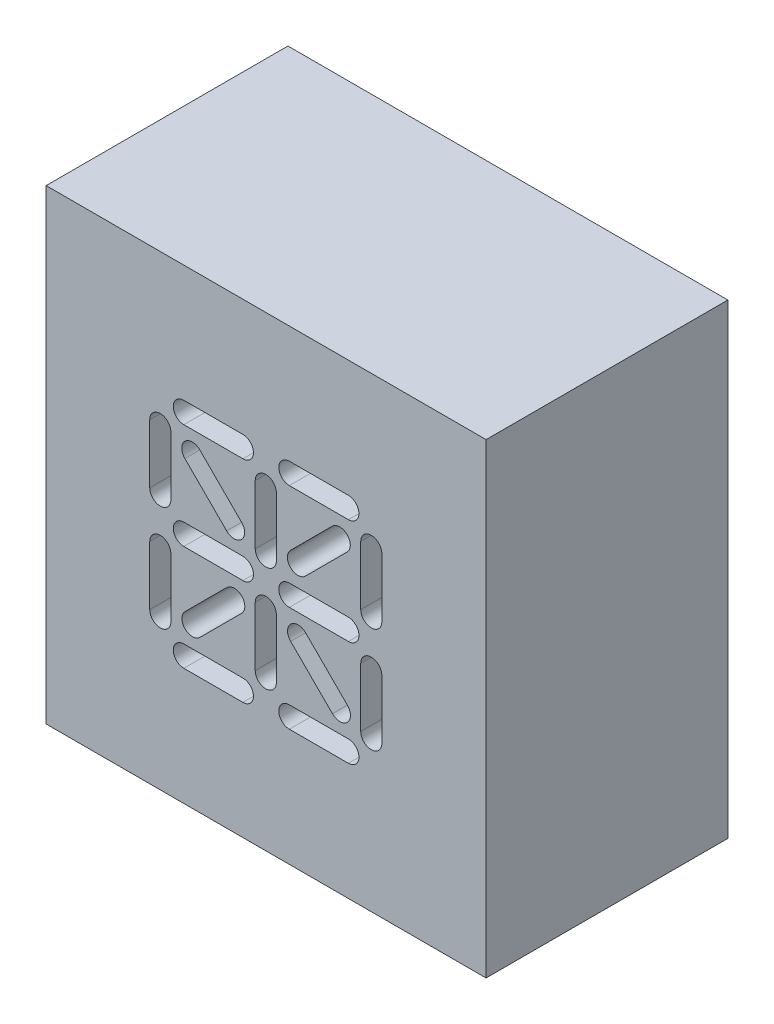
SolidWorks part; units mm, degrees
material "ABS PC"
ref_plane "Front Plane" through (0, 0, 0) normal (0, 0, 1) x (1, 0, 0)
ref_plane "Top Plane" through (0, 0, 0) normal (0, 1, 0) x (1, 0, 0)
ref_plane "Right Plane" through (0, 0, 0) normal (1, 0, 0) x (0, 0, -1)
sketch "Sketch1" plane through (0, 0, 0) normal (0, 0, 1) x (1, 0, 0)
  line L0 (265.9975, 197.0179) -> (342.1693, 194.9479) construction
  line L1 (297.418, 228.3826) -> (298.307, 228.3826) construction
  line L2 (297.418, 228.3826) -> (300.593, 228.3826) construction
  line L3 (302.371, 228.3826) -> (302.371, 231.5576) construction
  line L4 (296.7097, 229.0811) -> (296.7097, 229.9701) construction
  line L5 (296.7097, 230.8591) -> (296.7097, 234.0341) construction
  line L6 (296.7097, 234.0341) -> (299.8847, 234.0341) construction
  line L7 (296.7097, 234.0341) -> (297.0639, 234.3834) construction
  line L8 (296.7097, 234.0341) -> (297.418, 234.7326) construction
  line L9 (299.196, 231.5576) -> (300.593, 231.5576) construction
  line L10 (297.0639, 234.3834) -> (299.5404, 231.9069) construction
  line L11 (296.7097, 232.2561) -> (296.7097, 230.8591) construction
  line L12 (297.418, 231.5576) -> (296.7097, 231.5576) construction
  line L13 (299.8847, 232.2561) -> (299.196, 231.5576) construction
  line L14 (299.8945, 231.5576) -> (298.9307, 232.5165) construction
  line L15 (299.8945, 231.5576) -> (300.8534, 232.5214) construction
  line L16 (297.418, 234.7326) -> (307.578, 234.7326) construction
  line L17 (293.5347, 230.4146) -> (293.5347, 229.5256) construction
  line L18 (293.5347, 232.7006) -> (293.5347, 230.4146) construction
  line L19 (335.8892, 225.6039) -> (291.1852, 225.6039)
  line L20 (335.8892, 225.6039) -> (335.8892, 237.5114)
  line L21 (335.8892, 237.5114) -> (291.1852, 237.5114)
  line L22 (291.1852, 225.6039) -> (291.1852, 237.5114)
  line L23 (335.8892, 225.6039) -> (291.1852, 237.5114) construction
  line L24 (335.8892, 237.5114) -> (291.1852, 225.6039) construction
  line L25 (333.5397, 232.2561) -> (333.5397, 230.8591) construction
  line L26 (293.5347, 231.5576) -> (333.5397, 231.5576) construction
  line L27 (297.418, 228.3826) -> (299.196, 228.3826) construction
  line L32 (297.418, 228.7001) -> (299.196, 228.7001)
  line L33 (297.418, 228.0651) -> (299.196, 228.0651)
  line L34 (300.593, 228.3826) -> (302.371, 228.3826) construction
  line L35 (300.593, 228.7001) -> (302.371, 228.7001)
  line L36 (300.593, 228.0651) -> (302.371, 228.0651)
  line L37 (302.1155, 229.3415) -> (300.8582, 230.5987) construction
  line L38 (301.891, 229.117) -> (300.6337, 230.3742)
  line L39 (302.34, 229.566) -> (301.0827, 230.8233)
  line L40 (299.8847, 229.0811) -> (299.8847, 230.8591) construction
  line L41 (299.5672, 229.0811) -> (299.5672, 230.8591)
  line L42 (300.2022, 229.0811) -> (300.2022, 230.8591)
  line L43 (298.9356, 230.5939) -> (297.6784, 229.3366) construction
  line L44 (299.1601, 230.3694) -> (297.9029, 229.1121)
  line L45 (298.7111, 230.8184) -> (297.4539, 229.5611)
  line L46 (296.7097, 229.0811) -> (296.7097, 230.8591) construction
  line L47 (296.3922, 229.0811) -> (296.3922, 230.8591)
  line L48 (297.0272, 229.0811) -> (297.0272, 230.8591)
  line L49 (303.0597, 230.8591) -> (303.0597, 229.0811) construction
  line L50 (303.3772, 230.8591) -> (303.3772, 229.0811)
  line L51 (302.7422, 230.8591) -> (302.7422, 229.0811)
  line L52 (302.371, 231.5576) -> (300.593, 231.5576) construction
  line L53 (302.371, 231.2401) -> (300.593, 231.2401)
  line L54 (302.371, 231.8751) -> (300.593, 231.8751)
  line L55 (303.0597, 234.0341) -> (303.0597, 232.2561) construction
  line L56 (303.3772, 234.0341) -> (303.3772, 232.2561)
  line L57 (302.7422, 234.0341) -> (302.7422, 232.2561)
  line L58 (302.1106, 233.7786) -> (300.8534, 232.5214) construction
  line L59 (302.3351, 233.5541) -> (301.0779, 232.2969)
  line L60 (301.8861, 234.0031) -> (300.6289, 232.7459)
  line L61 (302.371, 234.7326) -> (300.593, 234.7326) construction
  line L62 (302.371, 234.4151) -> (300.593, 234.4151)
  line L63 (302.371, 235.0501) -> (300.593, 235.0501)
  line L64 (299.8847, 234.0341) -> (299.8847, 232.2561) construction
  line L65 (300.2022, 234.0341) -> (300.2022, 232.2561)
  line L66 (299.5672, 234.0341) -> (299.5672, 232.2561)
  line L67 (297.418, 231.5576) -> (299.196, 231.5576) construction
  line L68 (297.418, 231.8751) -> (299.196, 231.8751)
  line L69 (297.418, 231.2401) -> (299.196, 231.2401)
  line L70 (298.9307, 232.5165) -> (297.6735, 233.7737) construction
  line L71 (298.7062, 232.292) -> (297.449, 233.5492)
  line L72 (299.1552, 232.741) -> (297.898, 233.9983)
  line L73 (296.7097, 232.2561) -> (296.7097, 234.0341) construction
  line L74 (296.3922, 232.2561) -> (296.3922, 234.0341)
  line L75 (297.0272, 232.2561) -> (297.0272, 234.0341)
  line L76 (297.418, 234.7326) -> (299.196, 234.7326) construction
  line L77 (297.418, 235.0501) -> (299.196, 235.0501)
  line L78 (297.418, 234.4151) -> (299.196, 234.4151)
  line L79 (293.5347, 232.7006) -> (293.5347, 233.5896) construction
  line L80 (293.2172, 232.7006) -> (293.2172, 233.5896)
  line L81 (293.8522, 232.7006) -> (293.8522, 233.5896)
  line L82 (293.5347, 230.4146) -> (293.5347, 229.5256) construction
  line L83 (293.8522, 230.4146) -> (293.8522, 229.5256)
  line L84 (293.2172, 230.4146) -> (293.2172, 229.5256)
  line L85 (307.578, 228.3826) -> (309.356, 228.3826) construction
  line L86 (307.578, 228.7001) -> (309.356, 228.7001)
  line L87 (307.578, 228.0651) -> (309.356, 228.0651)
  line L88 (310.753, 228.3826) -> (312.531, 228.3826) construction
  line L89 (310.753, 228.7001) -> (312.531, 228.7001)
  line L90 (310.753, 228.0651) -> (312.531, 228.0651)
  line L91 (312.2755, 229.3415) -> (311.0182, 230.5987) construction
  line L92 (312.051, 229.117) -> (310.7937, 230.3742)
  line L93 (312.5, 229.566) -> (311.2427, 230.8233)
  line L94 (310.0447, 229.0811) -> (310.0447, 230.8591) construction
  line L95 (309.7272, 229.0811) -> (309.7272, 230.8591)
  line L96 (310.3622, 229.0811) -> (310.3622, 230.8591)
  line L97 (309.0956, 230.5939) -> (307.8384, 229.3366) construction
  line L98 (309.3201, 230.3694) -> (308.0629, 229.1121)
  line L99 (308.8711, 230.8184) -> (307.6139, 229.5611)
  line L100 (306.8697, 229.0811) -> (306.8697, 230.8591) construction
  line L101 (306.5522, 229.0811) -> (306.5522, 230.8591)
  line L102 (307.1872, 229.0811) -> (307.1872, 230.8591)
  line L103 (313.2197, 230.8591) -> (313.2197, 229.0811) construction
  line L104 (313.5372, 230.8591) -> (313.5372, 229.0811)
  line L105 (312.9022, 230.8591) -> (312.9022, 229.0811)
  line L106 (312.531, 231.5576) -> (310.753, 231.5576) construction
  line L107 (312.531, 231.2401) -> (310.753, 231.2401)
  line L108 (312.531, 231.8751) -> (310.753, 231.8751)
  line L109 (313.2197, 234.0341) -> (313.2197, 232.2561) construction
  line L110 (313.5372, 234.0341) -> (313.5372, 232.2561)
  line L111 (312.9022, 234.0341) -> (312.9022, 232.2561)
  line L112 (312.2706, 233.7786) -> (311.0134, 232.5214) construction
  line L113 (312.4951, 233.5541) -> (311.2379, 232.2969)
  line L114 (312.0461, 234.0031) -> (310.7889, 232.7459)
  line L115 (312.531, 234.7326) -> (310.753, 234.7326) construction
  line L116 (312.531, 234.4151) -> (310.753, 234.4151)
  line L117 (312.531, 235.0501) -> (310.753, 235.0501)
  line L118 (310.0447, 234.0341) -> (310.0447, 232.2561) construction
  line L119 (310.3622, 234.0341) -> (310.3622, 232.2561)
  line L120 (309.7272, 234.0341) -> (309.7272, 232.2561)
  line L121 (307.578, 231.5576) -> (309.356, 231.5576) construction
  line L122 (307.578, 231.8751) -> (309.356, 231.8751)
  line L123 (307.578, 231.2401) -> (309.356, 231.2401)
  line L124 (309.0907, 232.5165) -> (307.8335, 233.7737) construction
  line L125 (308.8662, 232.292) -> (307.609, 233.5492)
  line L126 (309.3152, 232.741) -> (308.058, 233.9983)
  line L127 (306.8697, 232.2561) -> (306.8697, 234.0341) construction
  line L128 (306.5522, 232.2561) -> (306.5522, 234.0341)
  line L129 (307.1872, 232.2561) -> (307.1872, 234.0341)
  line L130 (307.578, 234.7326) -> (309.356, 234.7326) construction
  line L131 (307.578, 235.0501) -> (309.356, 235.0501)
  line L132 (307.578, 234.4151) -> (309.356, 234.4151)
  line L133 (317.738, 228.3826) -> (319.516, 228.3826) construction
  line L134 (317.738, 228.7001) -> (319.516, 228.7001)
  line L135 (317.738, 228.0651) -> (319.516, 228.0651)
  line L136 (320.913, 228.3826) -> (322.691, 228.3826) construction
  line L137 (320.913, 228.7001) -> (322.691, 228.7001)
  line L138 (320.913, 228.0651) -> (322.691, 228.0651)
  line L139 (322.4355, 229.3415) -> (321.1782, 230.5987) construction
  line L140 (322.211, 229.117) -> (320.9537, 230.3742)
  line L141 (322.66, 229.566) -> (321.4027, 230.8233)
  line L142 (320.2047, 229.0811) -> (320.2047, 230.8591) construction
  line L143 (319.8872, 229.0811) -> (319.8872, 230.8591)
  line L144 (320.5222, 229.0811) -> (320.5222, 230.8591)
  line L145 (319.2556, 230.5939) -> (317.9984, 229.3366) construction
  line L146 (319.4801, 230.3694) -> (318.2229, 229.1121)
  line L147 (319.0311, 230.8184) -> (317.7739, 229.5611)
  line L148 (317.0297, 229.0811) -> (317.0297, 230.8591) construction
  line L149 (316.7122, 229.0811) -> (316.7122, 230.8591)
  line L150 (317.3472, 229.0811) -> (317.3472, 230.8591)
  line L151 (323.3797, 230.8591) -> (323.3797, 229.0811) construction
  line L152 (323.6972, 230.8591) -> (323.6972, 229.0811)
  line L153 (323.0622, 230.8591) -> (323.0622, 229.0811)
  line L154 (322.691, 231.5576) -> (320.913, 231.5576) construction
  line L155 (322.691, 231.2401) -> (320.913, 231.2401)
  line L156 (322.691, 231.8751) -> (320.913, 231.8751)
  line L157 (323.3797, 234.0341) -> (323.3797, 232.2561) construction
  line L158 (323.6972, 234.0341) -> (323.6972, 232.2561)
  line L159 (323.0622, 234.0341) -> (323.0622, 232.2561)
  line L160 (322.4306, 233.7786) -> (321.1734, 232.5214) construction
  line L161 (322.6551, 233.5541) -> (321.3979, 232.2969)
  line L162 (322.2061, 234.0031) -> (320.9489, 232.7459)
  line L163 (322.691, 234.7326) -> (320.913, 234.7326) construction
  line L164 (322.691, 234.4151) -> (320.913, 234.4151)
  line L165 (322.691, 235.0501) -> (320.913, 235.0501)
  line L166 (320.2047, 234.0341) -> (320.2047, 232.2561) construction
  line L167 (320.5222, 234.0341) -> (320.5222, 232.2561)
  line L168 (319.8872, 234.0341) -> (319.8872, 232.2561)
  line L169 (317.738, 231.5576) -> (319.516, 231.5576) construction
  line L170 (317.738, 231.8751) -> (319.516, 231.8751)
  line L171 (317.738, 231.2401) -> (319.516, 231.2401)
  line L172 (319.2507, 232.5165) -> (317.9935, 233.7737) construction
  line L173 (319.0262, 232.292) -> (317.769, 233.5492)
  line L174 (319.4752, 232.741) -> (318.218, 233.9983)
  line L175 (317.0297, 232.2561) -> (317.0297, 234.0341) construction
  line L176 (316.7122, 232.2561) -> (316.7122, 234.0341)
  line L177 (317.3472, 232.2561) -> (317.3472, 234.0341)
  line L178 (317.738, 234.7326) -> (319.516, 234.7326) construction
  line L179 (317.738, 235.0501) -> (319.516, 235.0501)
  line L180 (317.738, 234.4151) -> (319.516, 234.4151)
  line L181 (327.898, 228.3826) -> (329.676, 228.3826) construction
  line L182 (327.898, 228.7001) -> (329.676, 228.7001)
  line L183 (327.898, 228.0651) -> (329.676, 228.0651)
  line L184 (331.073, 228.3826) -> (332.851, 228.3826) construction
  line L185 (331.073, 228.7001) -> (332.851, 228.7001)
  line L186 (331.073, 228.0651) -> (332.851, 228.0651)
  line L187 (332.5955, 229.3415) -> (331.3382, 230.5987) construction
  line L188 (332.371, 229.117) -> (331.1137, 230.3742)
  line L189 (332.82, 229.566) -> (331.5627, 230.8233)
  line L190 (330.3647, 229.0811) -> (330.3647, 230.8591) construction
  line L191 (330.0472, 229.0811) -> (330.0472, 230.8591)
  line L192 (330.6822, 229.0811) -> (330.6822, 230.8591)
  line L193 (329.4156, 230.5939) -> (328.1584, 229.3366) construction
  line L194 (329.6401, 230.3694) -> (328.3829, 229.1121)
  line L195 (329.1911, 230.8184) -> (327.9339, 229.5611)
  line L196 (327.1897, 229.0811) -> (327.1897, 230.8591) construction
  line L197 (326.8722, 229.0811) -> (326.8722, 230.8591)
  line L198 (327.5072, 229.0811) -> (327.5072, 230.8591)
  line L199 (333.5397, 230.8591) -> (333.5397, 229.0811) construction
  line L200 (333.8572, 230.8591) -> (333.8572, 229.0811)
  line L201 (333.2222, 230.8591) -> (333.2222, 229.0811)
  line L202 (332.851, 231.5576) -> (331.073, 231.5576) construction
  line L203 (332.851, 231.2401) -> (331.073, 231.2401)
  line L204 (332.851, 231.8751) -> (331.073, 231.8751)
  line L205 (333.5397, 234.0341) -> (333.5397, 232.2561) construction
  line L206 (333.8572, 234.0341) -> (333.8572, 232.2561)
  line L207 (333.2222, 234.0341) -> (333.2222, 232.2561)
  line L208 (332.5906, 233.7786) -> (331.3334, 232.5214) construction
  line L209 (332.8151, 233.5541) -> (331.5579, 232.2969)
  line L210 (332.3661, 234.0031) -> (331.1089, 232.7459)
  line L211 (332.851, 234.7326) -> (331.073, 234.7326) construction
  line L212 (332.851, 234.4151) -> (331.073, 234.4151)
  line L213 (332.851, 235.0501) -> (331.073, 235.0501)
  line L214 (330.3647, 234.0341) -> (330.3647, 232.2561) construction
  line L215 (330.6822, 234.0341) -> (330.6822, 232.2561)
  line L216 (330.0472, 234.0341) -> (330.0472, 232.2561)
  line L217 (327.898, 231.5576) -> (329.676, 231.5576) construction
  line L218 (327.898, 231.8751) -> (329.676, 231.8751)
  line L219 (327.898, 231.2401) -> (329.676, 231.2401)
  line L220 (329.4107, 232.5165) -> (328.1535, 233.7737) construction
  line L221 (329.1862, 232.292) -> (327.929, 233.5492)
  line L222 (329.6352, 232.741) -> (328.378, 233.9983)
  line L223 (327.1897, 232.2561) -> (327.1897, 234.0341) construction
  line L224 (326.8722, 232.2561) -> (326.8722, 234.0341)
  line L225 (327.5072, 232.2561) -> (327.5072, 234.0341)
  line L226 (327.898, 234.7326) -> (329.676, 234.7326) construction
  line L227 (327.898, 235.0501) -> (329.676, 235.0501)
  line L228 (327.898, 234.4151) -> (329.676, 234.4151)
  line L229 (296.7097, 229.0811) -> (306.8697, 229.0811) construction
  circle A0 centre (297.418, 228.3826) radius 0.3175 construction
  circle A3 centre (298.307, 228.3826) radius 0.3175 construction
  circle A4 centre (299.196, 228.3826) radius 0.3175 construction
  circle A5 centre (300.593, 228.3826) radius 0.3175 construction
  circle A6 centre (301.482, 228.3826) radius 0.3175 construction
  circle A7 centre (302.371, 228.3826) radius 0.3175 construction
  circle A8 centre (302.371, 231.5576) radius 0.3175 construction
  circle A9 centre (301.482, 231.5576) radius 0.3175 construction
  circle A10 centre (300.593, 231.5576) radius 0.3175 construction
  circle A11 centre (299.196, 231.5576) radius 0.3175 construction
  circle A12 centre (298.307, 231.5576) radius 0.3175 construction
  circle A13 centre (297.418, 231.5576) radius 0.3175 construction
  circle A14 centre (302.371, 234.7326) radius 0.3175 construction
  circle A15 centre (301.482, 234.7326) radius 0.3175 construction
  circle A16 centre (300.593, 234.7326) radius 0.3175 construction
  circle A17 centre (299.196, 234.7326) radius 0.3175 construction
  circle A18 centre (298.307, 234.7326) radius 0.3175 construction
  circle A19 centre (297.418, 234.7326) radius 0.3175 construction
  circle A20 centre (296.7097, 229.0811) radius 0.3175 construction
  circle A21 centre (296.7097, 229.9701) radius 0.3175 construction
  circle A22 centre (296.7097, 230.8591) radius 0.3175 construction
  circle A23 centre (296.7097, 234.0341) radius 0.3175 construction
  circle A24 centre (296.7097, 233.1451) radius 0.3175 construction
  circle A25 centre (296.7097, 232.2561) radius 0.3175 construction
  circle A26 centre (299.8847, 234.0341) radius 0.3175 construction
  circle A27 centre (299.8847, 233.1451) radius 0.3175 construction
  circle A28 centre (299.8847, 232.2561) radius 0.3175 construction
  circle A29 centre (299.8847, 230.8591) radius 0.3175 construction
  circle A30 centre (299.8847, 229.9701) radius 0.3175 construction
  circle A31 centre (299.8847, 229.0811) radius 0.3175 construction
  circle A32 centre (297.6735, 233.7737) radius 0.3175 construction
  circle A33 centre (298.3021, 233.1451) radius 0.3175 construction
  circle A34 centre (298.9307, 232.5165) radius 0.3175 construction
  circle A35 centre (303.0597, 234.0341) radius 0.3175 construction
  circle A36 centre (303.0597, 233.1451) radius 0.3175 construction
  circle A37 centre (303.0597, 232.2561) radius 0.3175 construction
  circle A38 centre (303.0597, 230.8591) radius 0.3175 construction
  circle A39 centre (303.0597, 229.9701) radius 0.3175 construction
  circle A40 centre (303.0597, 229.0811) radius 0.3175 construction
  circle A41 centre (300.8534, 232.5214) radius 0.3175 construction
  circle A42 centre (301.482, 233.15) radius 0.3175 construction
  circle A43 centre (302.1106, 233.7786) radius 0.3175 construction
  circle A44 centre (300.8582, 230.5987) radius 0.3175 construction
  circle A45 centre (301.4869, 229.9701) radius 0.3175 construction
  circle A46 centre (302.1155, 229.3415) radius 0.3175 construction
  circle A47 centre (298.9356, 230.5939) radius 0.3175 construction
  circle A48 centre (298.307, 229.9653) radius 0.3175 construction
  circle A49 centre (297.6784, 229.3366) radius 0.3175 construction
  circle A50 centre (307.578, 234.7326) radius 0.3175 construction
  circle A51 centre (306.8697, 234.0341) radius 0.3175 construction
  circle A52 centre (306.8697, 233.1451) radius 0.3175 construction
  circle A53 centre (306.8697, 232.2561) radius 0.3175 construction
  circle A54 centre (308.467, 234.7326) radius 0.3175 construction
  circle A55 centre (309.356, 234.7326) radius 0.3175 construction
  circle A56 centre (310.753, 234.7326) radius 0.3175 construction
  circle A57 centre (311.642, 234.7326) radius 0.3175 construction
  circle A58 centre (312.531, 234.7326) radius 0.3175 construction
  circle A59 centre (313.2197, 234.0341) radius 0.3175 construction
  circle A60 centre (313.2197, 233.1451) radius 0.3175 construction
  circle A61 centre (313.2197, 232.2561) radius 0.3175 construction
  circle A62 centre (313.2197, 230.8591) radius 0.3175 construction
  circle A63 centre (313.2197, 229.9701) radius 0.3175 construction
  circle A64 centre (313.2197, 229.0811) radius 0.3175 construction
  circle A65 centre (312.531, 228.3826) radius 0.3175 construction
  circle A66 centre (311.642, 228.3826) radius 0.3175 construction
  circle A67 centre (310.753, 228.3826) radius 0.3175 construction
  circle A68 centre (309.356, 228.3826) radius 0.3175 construction
  circle A69 centre (308.467, 228.3826) radius 0.3175 construction
  circle A70 centre (307.578, 228.3826) radius 0.3175 construction
  circle A71 centre (306.8697, 229.0811) radius 0.3175 construction
  circle A72 centre (306.8697, 229.9701) radius 0.3175 construction
  circle A73 centre (306.8697, 230.8591) radius 0.3175 construction
  circle A74 centre (307.578, 231.5576) radius 0.3175 construction
  circle A75 centre (308.467, 231.5576) radius 0.3175 construction
  circle A76 centre (309.356, 231.5576) radius 0.3175 construction
  circle A77 centre (310.753, 231.5576) radius 0.3175 construction
  circle A78 centre (311.642, 231.5576) radius 0.3175 construction
  circle A79 centre (312.531, 231.5576) radius 0.3175 construction
  circle A80 centre (312.2706, 233.7786) radius 0.3175 construction
  circle A81 centre (311.642, 233.15) radius 0.3175 construction
  circle A82 centre (311.0134, 232.5214) radius 0.3175 construction
  circle A83 centre (310.0447, 232.2561) radius 0.3175 construction
  circle A84 centre (310.0447, 233.1451) radius 0.3175 construction
  circle A85 centre (310.0447, 234.0341) radius 0.3175 construction
  circle A86 centre (309.0907, 232.5165) radius 0.3175 construction
  circle A87 centre (308.4621, 233.1451) radius 0.3175 construction
  circle A88 centre (307.8335, 233.7737) radius 0.3175 construction
  circle A89 centre (307.8384, 229.3366) radius 0.3175 construction
  circle A90 centre (308.467, 229.9653) radius 0.3175 construction
  circle A91 centre (309.0956, 230.5939) radius 0.3175 construction
  circle A92 centre (310.0447, 230.8591) radius 0.3175 construction
  circle A93 centre (310.0447, 229.9701) radius 0.3175 construction
  circle A94 centre (310.0447, 229.0811) radius 0.3175 construction
  circle A95 centre (312.2755, 229.3415) radius 0.3175 construction
  circle A96 centre (311.6469, 229.9701) radius 0.3175 construction
  circle A97 centre (311.0182, 230.5987) radius 0.3175 construction
  circle A98 centre (317.738, 234.7326) radius 0.3175 construction
  circle A99 centre (317.0297, 234.0341) radius 0.3175 construction
  circle A100 centre (317.0297, 233.1451) radius 0.3175 construction
  circle A101 centre (317.0297, 232.2561) radius 0.3175 construction
  circle A102 centre (318.627, 234.7326) radius 0.3175 construction
  circle A103 centre (319.516, 234.7326) radius 0.3175 construction
  circle A104 centre (320.913, 234.7326) radius 0.3175 construction
  circle A105 centre (321.802, 234.7326) radius 0.3175 construction
  circle A106 centre (322.691, 234.7326) radius 0.3175 construction
  circle A107 centre (323.3797, 234.0341) radius 0.3175 construction
  circle A108 centre (323.3797, 233.1451) radius 0.3175 construction
  circle A109 centre (323.3797, 232.2561) radius 0.3175 construction
  circle A110 centre (323.3797, 230.8591) radius 0.3175 construction
  circle A111 centre (323.3797, 229.9701) radius 0.3175 construction
  circle A112 centre (323.3797, 229.0811) radius 0.3175 construction
  circle A113 centre (322.691, 228.3826) radius 0.3175 construction
  circle A114 centre (321.802, 228.3826) radius 0.3175 construction
  circle A115 centre (320.913, 228.3826) radius 0.3175 construction
  circle A116 centre (319.516, 228.3826) radius 0.3175 construction
  circle A117 centre (318.627, 228.3826) radius 0.3175 construction
  circle A118 centre (317.738, 228.3826) radius 0.3175 construction
  circle A119 centre (317.0297, 229.0811) radius 0.3175 construction
  circle A120 centre (317.0297, 229.9701) radius 0.3175 construction
  circle A121 centre (317.0297, 230.8591) radius 0.3175 construction
  circle A122 centre (317.738, 231.5576) radius 0.3175 construction
  circle A123 centre (318.627, 231.5576) radius 0.3175 construction
  circle A124 centre (319.516, 231.5576) radius 0.3175 construction
  circle A125 centre (320.913, 231.5576) radius 0.3175 construction
  circle A126 centre (321.802, 231.5576) radius 0.3175 construction
  circle A127 centre (322.691, 231.5576) radius 0.3175 construction
  circle A128 centre (322.4306, 233.7786) radius 0.3175 construction
  circle A129 centre (321.802, 233.15) radius 0.3175 construction
  circle A130 centre (321.1734, 232.5214) radius 0.3175 construction
  circle A131 centre (320.2047, 232.2561) radius 0.3175 construction
  circle A132 centre (320.2047, 233.1451) radius 0.3175 construction
  circle A133 centre (320.2047, 234.0341) radius 0.3175 construction
  circle A134 centre (319.2507, 232.5165) radius 0.3175 construction
  circle A135 centre (318.6221, 233.1451) radius 0.3175 construction
  circle A136 centre (317.9935, 233.7737) radius 0.3175 construction
  circle A137 centre (317.9984, 229.3366) radius 0.3175 construction
  circle A138 centre (318.627, 229.9653) radius 0.3175 construction
  circle A139 centre (319.2556, 230.5939) radius 0.3175 construction
  circle A140 centre (320.2047, 230.8591) radius 0.3175 construction
  circle A141 centre (320.2047, 229.9701) radius 0.3175 construction
  circle A142 centre (320.2047, 229.0811) radius 0.3175 construction
  circle A143 centre (322.4355, 229.3415) radius 0.3175 construction
  circle A144 centre (321.8069, 229.9701) radius 0.3175 construction
  circle A145 centre (321.1782, 230.5987) radius 0.3175 construction
  circle A146 centre (327.898, 234.7326) radius 0.3175 construction
  circle A147 centre (327.1897, 234.0341) radius 0.3175 construction
  circle A148 centre (327.1897, 233.1451) radius 0.3175 construction
  circle A149 centre (327.1897, 232.2561) radius 0.3175 construction
  circle A150 centre (328.787, 234.7326) radius 0.3175 construction
  circle A151 centre (329.676, 234.7326) radius 0.3175 construction
  circle A152 centre (331.073, 234.7326) radius 0.3175 construction
  circle A153 centre (331.962, 234.7326) radius 0.3175 construction
  circle A154 centre (332.851, 234.7326) radius 0.3175 construction
  circle A155 centre (333.5397, 234.0341) radius 0.3175 construction
  circle A156 centre (333.5397, 233.1451) radius 0.3175 construction
  circle A157 centre (333.5397, 232.2561) radius 0.3175 construction
  circle A158 centre (333.5397, 230.8591) radius 0.3175 construction
  circle A159 centre (333.5397, 229.9701) radius 0.3175 construction
  circle A160 centre (333.5397, 229.0811) radius 0.3175 construction
  circle A161 centre (332.851, 228.3826) radius 0.3175 construction
  circle A162 centre (331.962, 228.3826) radius 0.3175 construction
  circle A163 centre (331.073, 228.3826) radius 0.3175 construction
  circle A164 centre (329.676, 228.3826) radius 0.3175 construction
  circle A165 centre (328.787, 228.3826) radius 0.3175 construction
  circle A166 centre (327.898, 228.3826) radius 0.3175 construction
  circle A167 centre (327.1897, 229.0811) radius 0.3175 construction
  circle A168 centre (327.1897, 229.9701) radius 0.3175 construction
  circle A169 centre (327.1897, 230.8591) radius 0.3175 construction
  circle A170 centre (327.898, 231.5576) radius 0.3175 construction
  circle A171 centre (328.787, 231.5576) radius 0.3175 construction
  circle A172 centre (329.676, 231.5576) radius 0.3175 construction
  circle A173 centre (331.073, 231.5576) radius 0.3175 construction
  circle A174 centre (331.962, 231.5576) radius 0.3175 construction
  circle A175 centre (332.851, 231.5576) radius 0.3175 construction
  circle A176 centre (332.5906, 233.7786) radius 0.3175 construction
  circle A177 centre (331.962, 233.15) radius 0.3175 construction
  circle A178 centre (331.3334, 232.5214) radius 0.3175 construction
  circle A179 centre (330.3647, 232.2561) radius 0.3175 construction
  circle A180 centre (330.3647, 233.1451) radius 0.3175 construction
  circle A181 centre (330.3647, 234.0341) radius 0.3175 construction
  circle A182 centre (329.4107, 232.5165) radius 0.3175 construction
  circle A183 centre (328.7821, 233.1451) radius 0.3175 construction
  circle A184 centre (328.1535, 233.7737) radius 0.3175 construction
  circle A185 centre (328.1584, 229.3366) radius 0.3175 construction
  circle A186 centre (328.787, 229.9653) radius 0.3175 construction
  circle A187 centre (329.4156, 230.5939) radius 0.3175 construction
  circle A188 centre (330.3647, 230.8591) radius 0.3175 construction
  circle A189 centre (330.3647, 229.9701) radius 0.3175 construction
  circle A190 centre (330.3647, 229.0811) radius 0.3175 construction
  circle A191 centre (332.5955, 229.3415) radius 0.3175 construction
  circle A192 centre (331.9669, 229.9701) radius 0.3175 construction
  circle A193 centre (331.3382, 230.5987) radius 0.3175 construction
  circle A194 centre (293.5347, 229.5256) radius 0.3175 construction
  circle A195 centre (293.5347, 230.4146) radius 0.3175 construction
  circle A196 centre (293.5347, 233.5896) radius 0.3175 construction
  circle A197 centre (293.5347, 232.7006) radius 0.3175 construction
  arc A198 (297.418, 228.7001) -> (297.418, 228.0651) centre (297.418, 228.3826) ccw
  arc A199 (299.196, 228.0651) -> (299.196, 228.7001) centre (299.196, 228.3826) ccw
  arc A200 (300.593, 228.7001) -> (300.593, 228.0651) centre (300.593, 228.3826) ccw
  arc A201 (302.371, 228.0651) -> (302.371, 228.7001) centre (302.371, 228.3826) ccw
  arc A202 (301.891, 229.117) -> (302.34, 229.566) centre (302.1155, 229.3415) ccw
  arc A203 (301.0827, 230.8233) -> (300.6337, 230.3742) centre (300.8582, 230.5987) ccw
  arc A204 (299.5672, 229.0811) -> (300.2022, 229.0811) centre (299.8847, 229.0811) ccw
  arc A205 (300.2022, 230.8591) -> (299.5672, 230.8591) centre (299.8847, 230.8591) ccw
  arc A206 (299.1601, 230.3694) -> (298.7111, 230.8184) centre (298.9356, 230.5939) ccw
  arc A207 (297.4539, 229.5611) -> (297.9029, 229.1121) centre (297.6784, 229.3366) ccw
  arc A208 (296.3922, 229.0811) -> (297.0272, 229.0811) centre (296.7097, 229.0811) ccw
  arc A209 (297.0272, 230.8591) -> (296.3922, 230.8591) centre (296.7097, 230.8591) ccw
  arc A210 (303.3772, 230.8591) -> (302.7422, 230.8591) centre (303.0597, 230.8591) ccw
  arc A211 (302.7422, 229.0811) -> (303.3772, 229.0811) centre (303.0597, 229.0811) ccw
  arc A212 (302.371, 231.2401) -> (302.371, 231.8751) centre (302.371, 231.5576) ccw
  arc A213 (300.593, 231.8751) -> (300.593, 231.2401) centre (300.593, 231.5576) ccw
  arc A214 (303.3772, 234.0341) -> (302.7422, 234.0341) centre (303.0597, 234.0341) ccw
  arc A215 (302.7422, 232.2561) -> (303.3772, 232.2561) centre (303.0597, 232.2561) ccw
  arc A216 (302.3351, 233.5541) -> (301.8861, 234.0031) centre (302.1106, 233.7786) ccw
  arc A217 (300.6289, 232.7459) -> (301.0779, 232.2969) centre (300.8534, 232.5214) ccw
  arc A218 (302.371, 234.4151) -> (302.371, 235.0501) centre (302.371, 234.7326) ccw
  arc A219 (300.593, 235.0501) -> (300.593, 234.4151) centre (300.593, 234.7326) ccw
  arc A220 (300.2022, 234.0341) -> (299.5672, 234.0341) centre (299.8847, 234.0341) ccw
  arc A221 (299.5672, 232.2561) -> (300.2022, 232.2561) centre (299.8847, 232.2561) ccw
  arc A222 (297.418, 231.8751) -> (297.418, 231.2401) centre (297.418, 231.5576) ccw
  arc A223 (299.196, 231.2401) -> (299.196, 231.8751) centre (299.196, 231.5576) ccw
  arc A224 (298.7062, 232.292) -> (299.1552, 232.741) centre (298.9307, 232.5165) ccw
  arc A225 (297.898, 233.9983) -> (297.449, 233.5492) centre (297.6735, 233.7737) ccw
  arc A226 (296.3922, 232.2561) -> (297.0272, 232.2561) centre (296.7097, 232.2561) ccw
  arc A227 (297.0272, 234.0341) -> (296.3922, 234.0341) centre (296.7097, 234.0341) ccw
  arc A228 (297.418, 235.0501) -> (297.418, 234.4151) centre (297.418, 234.7326) ccw
  arc A229 (299.196, 234.4151) -> (299.196, 235.0501) centre (299.196, 234.7326) ccw
  arc A230 (293.2172, 232.7006) -> (293.8522, 232.7006) centre (293.5347, 232.7006) ccw
  arc A231 (293.8522, 233.5896) -> (293.2172, 233.5896) centre (293.5347, 233.5896) ccw
  arc A232 (293.8522, 230.4146) -> (293.2172, 230.4146) centre (293.5347, 230.4146) ccw
  arc A233 (293.2172, 229.5256) -> (293.8522, 229.5256) centre (293.5347, 229.5256) ccw
  arc A234 (307.578, 228.7001) -> (307.578, 228.0651) centre (307.578, 228.3826) ccw
  arc A235 (309.356, 228.0651) -> (309.356, 228.7001) centre (309.356, 228.3826) ccw
  arc A236 (310.753, 228.7001) -> (310.753, 228.0651) centre (310.753, 228.3826) ccw
  arc A237 (312.531, 228.0651) -> (312.531, 228.7001) centre (312.531, 228.3826) ccw
  arc A238 (312.051, 229.117) -> (312.5, 229.566) centre (312.2755, 229.3415) ccw
  arc A239 (311.2427, 230.8233) -> (310.7937, 230.3742) centre (311.0182, 230.5987) ccw
  arc A240 (309.7272, 229.0811) -> (310.3622, 229.0811) centre (310.0447, 229.0811) ccw
  arc A241 (310.3622, 230.8591) -> (309.7272, 230.8591) centre (310.0447, 230.8591) ccw
  arc A242 (309.3201, 230.3694) -> (308.8711, 230.8184) centre (309.0956, 230.5939) ccw
  arc A243 (307.6139, 229.5611) -> (308.0629, 229.1121) centre (307.8384, 229.3366) ccw
  arc A244 (306.5522, 229.0811) -> (307.1872, 229.0811) centre (306.8697, 229.0811) ccw
  arc A245 (307.1872, 230.8591) -> (306.5522, 230.8591) centre (306.8697, 230.8591) ccw
  arc A246 (313.5372, 230.8591) -> (312.9022, 230.8591) centre (313.2197, 230.8591) ccw
  arc A247 (312.9022, 229.0811) -> (313.5372, 229.0811) centre (313.2197, 229.0811) ccw
  arc A248 (312.531, 231.2401) -> (312.531, 231.8751) centre (312.531, 231.5576) ccw
  arc A249 (310.753, 231.8751) -> (310.753, 231.2401) centre (310.753, 231.5576) ccw
  arc A250 (313.5372, 234.0341) -> (312.9022, 234.0341) centre (313.2197, 234.0341) ccw
  arc A251 (312.9022, 232.2561) -> (313.5372, 232.2561) centre (313.2197, 232.2561) ccw
  arc A252 (312.4951, 233.5541) -> (312.0461, 234.0031) centre (312.2706, 233.7786) ccw
  arc A253 (310.7889, 232.7459) -> (311.2379, 232.2969) centre (311.0134, 232.5214) ccw
  arc A254 (312.531, 234.4151) -> (312.531, 235.0501) centre (312.531, 234.7326) ccw
  arc A255 (310.753, 235.0501) -> (310.753, 234.4151) centre (310.753, 234.7326) ccw
  arc A256 (310.3622, 234.0341) -> (309.7272, 234.0341) centre (310.0447, 234.0341) ccw
  arc A257 (309.7272, 232.2561) -> (310.3622, 232.2561) centre (310.0447, 232.2561) ccw
  arc A258 (307.578, 231.8751) -> (307.578, 231.2401) centre (307.578, 231.5576) ccw
  arc A259 (309.356, 231.2401) -> (309.356, 231.8751) centre (309.356, 231.5576) ccw
  arc A260 (308.8662, 232.292) -> (309.3152, 232.741) centre (309.0907, 232.5165) ccw
  arc A261 (308.058, 233.9983) -> (307.609, 233.5492) centre (307.8335, 233.7737) ccw
  arc A262 (306.5522, 232.2561) -> (307.1872, 232.2561) centre (306.8697, 232.2561) ccw
  arc A263 (307.1872, 234.0341) -> (306.5522, 234.0341) centre (306.8697, 234.0341) ccw
  arc A264 (307.578, 235.0501) -> (307.578, 234.4151) centre (307.578, 234.7326) ccw
  arc A265 (309.356, 234.4151) -> (309.356, 235.0501) centre (309.356, 234.7326) ccw
  arc A266 (317.738, 228.7001) -> (317.738, 228.0651) centre (317.738, 228.3826) ccw
  arc A267 (319.516, 228.0651) -> (319.516, 228.7001) centre (319.516, 228.3826) ccw
  arc A268 (320.913, 228.7001) -> (320.913, 228.0651) centre (320.913, 228.3826) ccw
  arc A269 (322.691, 228.0651) -> (322.691, 228.7001) centre (322.691, 228.3826) ccw
  arc A270 (322.211, 229.117) -> (322.66, 229.566) centre (322.4355, 229.3415) ccw
  arc A271 (321.4027, 230.8233) -> (320.9537, 230.3742) centre (321.1782, 230.5987) ccw
  arc A272 (319.8872, 229.0811) -> (320.5222, 229.0811) centre (320.2047, 229.0811) ccw
  arc A273 (320.5222, 230.8591) -> (319.8872, 230.8591) centre (320.2047, 230.8591) ccw
  arc A274 (319.4801, 230.3694) -> (319.0311, 230.8184) centre (319.2556, 230.5939) ccw
  arc A275 (317.7739, 229.5611) -> (318.2229, 229.1121) centre (317.9984, 229.3366) ccw
  arc A276 (316.7122, 229.0811) -> (317.3472, 229.0811) centre (317.0297, 229.0811) ccw
  arc A277 (317.3472, 230.8591) -> (316.7122, 230.8591) centre (317.0297, 230.8591) ccw
  arc A278 (323.6972, 230.8591) -> (323.0622, 230.8591) centre (323.3797, 230.8591) ccw
  arc A279 (323.0622, 229.0811) -> (323.6972, 229.0811) centre (323.3797, 229.0811) ccw
  arc A280 (322.691, 231.2401) -> (322.691, 231.8751) centre (322.691, 231.5576) ccw
  arc A281 (320.913, 231.8751) -> (320.913, 231.2401) centre (320.913, 231.5576) ccw
  arc A282 (323.6972, 234.0341) -> (323.0622, 234.0341) centre (323.3797, 234.0341) ccw
  arc A283 (323.0622, 232.2561) -> (323.6972, 232.2561) centre (323.3797, 232.2561) ccw
  arc A284 (322.6551, 233.5541) -> (322.2061, 234.0031) centre (322.4306, 233.7786) ccw
  arc A285 (320.9489, 232.7459) -> (321.3979, 232.2969) centre (321.1734, 232.5214) ccw
  arc A286 (322.691, 234.4151) -> (322.691, 235.0501) centre (322.691, 234.7326) ccw
  arc A287 (320.913, 235.0501) -> (320.913, 234.4151) centre (320.913, 234.7326) ccw
  arc A288 (320.5222, 234.0341) -> (319.8872, 234.0341) centre (320.2047, 234.0341) ccw
  arc A289 (319.8872, 232.2561) -> (320.5222, 232.2561) centre (320.2047, 232.2561) ccw
  arc A290 (317.738, 231.8751) -> (317.738, 231.2401) centre (317.738, 231.5576) ccw
  arc A291 (319.516, 231.2401) -> (319.516, 231.8751) centre (319.516, 231.5576) ccw
  arc A292 (319.0262, 232.292) -> (319.4752, 232.741) centre (319.2507, 232.5165) ccw
  arc A293 (318.218, 233.9983) -> (317.769, 233.5492) centre (317.9935, 233.7737) ccw
  arc A294 (316.7122, 232.2561) -> (317.3472, 232.2561) centre (317.0297, 232.2561) ccw
  arc A295 (317.3472, 234.0341) -> (316.7122, 234.0341) centre (317.0297, 234.0341) ccw
  arc A296 (317.738, 235.0501) -> (317.738, 234.4151) centre (317.738, 234.7326) ccw
  arc A297 (319.516, 234.4151) -> (319.516, 235.0501) centre (319.516, 234.7326) ccw
  arc A298 (327.898, 228.7001) -> (327.898, 228.0651) centre (327.898, 228.3826) ccw
  arc A299 (329.676, 228.0651) -> (329.676, 228.7001) centre (329.676, 228.3826) ccw
  arc A300 (331.073, 228.7001) -> (331.073, 228.0651) centre (331.073, 228.3826) ccw
  arc A301 (332.851, 228.0651) -> (332.851, 228.7001) centre (332.851, 228.3826) ccw
  arc A302 (332.371, 229.117) -> (332.82, 229.566) centre (332.5955, 229.3415) ccw
  arc A303 (331.5627, 230.8233) -> (331.1137, 230.3742) centre (331.3382, 230.5987) ccw
  arc A304 (330.0472, 229.0811) -> (330.6822, 229.0811) centre (330.3647, 229.0811) ccw
  arc A305 (330.6822, 230.8591) -> (330.0472, 230.8591) centre (330.3647, 230.8591) ccw
  arc A306 (329.6401, 230.3694) -> (329.1911, 230.8184) centre (329.4156, 230.5939) ccw
  arc A307 (327.9339, 229.5611) -> (328.3829, 229.1121) centre (328.1584, 229.3366) ccw
  arc A308 (326.8722, 229.0811) -> (327.5072, 229.0811) centre (327.1897, 229.0811) ccw
  arc A309 (327.5072, 230.8591) -> (326.8722, 230.8591) centre (327.1897, 230.8591) ccw
  arc A310 (333.8572, 230.8591) -> (333.2222, 230.8591) centre (333.5397, 230.8591) ccw
  arc A311 (333.2222, 229.0811) -> (333.8572, 229.0811) centre (333.5397, 229.0811) ccw
  arc A312 (332.851, 231.2401) -> (332.851, 231.8751) centre (332.851, 231.5576) ccw
  arc A313 (331.073, 231.8751) -> (331.073, 231.2401) centre (331.073, 231.5576) ccw
  arc A314 (333.8572, 234.0341) -> (333.2222, 234.0341) centre (333.5397, 234.0341) ccw
  arc A315 (333.2222, 232.2561) -> (333.8572, 232.2561) centre (333.5397, 232.2561) ccw
  arc A316 (332.8151, 233.5541) -> (332.3661, 234.0031) centre (332.5906, 233.7786) ccw
  arc A317 (331.1089, 232.7459) -> (331.5579, 232.2969) centre (331.3334, 232.5214) ccw
  arc A318 (332.851, 234.4151) -> (332.851, 235.0501) centre (332.851, 234.7326) ccw
  arc A319 (331.073, 235.0501) -> (331.073, 234.4151) centre (331.073, 234.7326) ccw
  arc A320 (330.6822, 234.0341) -> (330.0472, 234.0341) centre (330.3647, 234.0341) ccw
  arc A321 (330.0472, 232.2561) -> (330.6822, 232.2561) centre (330.3647, 232.2561) ccw
  arc A322 (327.898, 231.8751) -> (327.898, 231.2401) centre (327.898, 231.5576) ccw
  arc A323 (329.676, 231.2401) -> (329.676, 231.8751) centre (329.676, 231.5576) ccw
  arc A324 (329.1862, 232.292) -> (329.6352, 232.741) centre (329.4107, 232.5165) ccw
  arc A325 (328.378, 233.9983) -> (327.929, 233.5492) centre (328.1535, 233.7737) ccw
  arc A326 (326.8722, 232.2561) -> (327.5072, 232.2561) centre (327.1897, 232.2561) ccw
  arc A327 (327.5072, 234.0341) -> (326.8722, 234.0341) centre (327.1897, 234.0341) ccw
  arc A328 (327.898, 235.0501) -> (327.898, 234.4151) centre (327.898, 234.7326) ccw
  arc A329 (329.676, 234.4151) -> (329.676, 235.0501) centre (329.676, 234.7326) ccw
  point P17 (298.307, 228.3826)
  point P81 (299.8945, 231.5576)
  point P96 (298.3021, 233.1451)
  point P410 (293.5347, 229.9701)
  point P411 (313.5372, 231.5576)
  point P422 (313.5372, 231.5576)
  point P426 (301.482, 228.3826)
  point P431 (301.4869, 229.9701)
  point P436 (299.8847, 229.9701)
  point P441 (298.307, 229.9653)
  point P446 (296.7097, 229.9701)
  point P451 (303.0597, 229.9701)
  point P456 (301.482, 231.5576)
  point P461 (303.0597, 233.1451)
  point P466 (301.482, 233.15)
  point P471 (301.482, 234.7326)
  point P476 (299.8847, 233.1451)
  point P481 (298.307, 231.5576)
  point P486 (298.3021, 233.1451)
  point P491 (296.7097, 233.1451)
  point P496 (298.307, 234.7326)
  point P501 (293.5347, 233.1451)
  point P506 (293.5347, 229.9701)
  point P518 (308.467, 228.3826)
  point P550 (311.642, 228.3826)
  point P555 (311.6469, 229.9701)
  point P560 (310.0447, 229.9701)
  point P565 (308.467, 229.9653)
  point P570 (306.8697, 229.9701)
  point P575 (313.2197, 229.9701)
  point P580 (311.642, 231.5576)
  point P585 (313.2197, 233.1451)
  point P590 (311.642, 233.15)
  point P595 (311.642, 234.7326)
  point P600 (310.0447, 233.1451)
  point P605 (308.467, 231.5576)
  point P610 (308.4621, 233.1451)
  point P615 (306.8697, 233.1451)
  point P620 (308.467, 234.7326)
  point P630 (318.627, 228.3826)
  point P662 (321.802, 228.3826)
  point P667 (321.8069, 229.9701)
  point P672 (320.2047, 229.9701)
  point P677 (318.627, 229.9653)
  point P682 (317.0297, 229.9701)
  point P687 (323.3797, 229.9701)
  point P692 (321.802, 231.5576)
  point P697 (323.3797, 233.1451)
  point P702 (321.802, 233.15)
  point P707 (321.802, 234.7326)
  point P712 (320.2047, 233.1451)
  point P717 (318.627, 231.5576)
  point P722 (318.6221, 233.1451)
  point P727 (317.0297, 233.1451)
  point P732 (318.627, 234.7326)
  point P742 (328.787, 228.3826)
  point P774 (331.962, 228.3826)
  point P779 (331.9669, 229.9701)
  point P784 (330.3647, 229.9701)
  point P789 (328.787, 229.9653)
  point P794 (327.1897, 229.9701)
  point P799 (333.5397, 229.9701)
  point P804 (331.962, 231.5576)
  point P809 (333.5397, 233.1451)
  point P814 (331.962, 233.15)
  point P819 (331.962, 234.7326)
  point P824 (330.3647, 233.1451)
  point P829 (328.787, 231.5576)
  point P834 (328.7821, 233.1451)
  point P839 (327.1897, 233.1451)
  point P844 (328.787, 234.7326)
  dimension "D2" = 0.635
  dimension "D1" = 76.2
  dimension "D4" = 0.889
  dimension "D6" = 3.175
  dimension "D8" = 3.175
  dimension "D10" = 0.889
  dimension "D12" = 3.175
  dimension "D14" = 3.175
  dimension "D15" = 0.7082
  dimension "D16" = 0.889
  dimension "D17" = 0.889
  dimension "D19" = 90
  dimension "D20" = 1.3595
  dimension "D22" = 10.16
  dimension "D23" = 0.889
  dimension "D24" = 3.175
  dimension "D25" = 11.9075
  dimension "D26" = 44.704
  dimension "D27" = 4
  dimension "D28" = 10.16
  dimension "D3" = 3
  dimension "D5" = 2
  dimension "D7" = 3
  dimension "D9" = 3
  dimension "D11" = 2
  dimension "D13" = 3
  dimension "D21" = 4
  dimension "D18" = 4
extrude "Boss-Extrude1" add sketch "Sketch1" along normal blind 7.2771 contours L22 L19 L20 L21 A196 A195 A194 A193 A192 A191 A190 A189 A188 A187 A186 A185 A184 A183 A182 A181 A180 A179 A178 A177 A176 A175 A174
pattern_linear "LPattern1" count 5 spacing 20.32 along (0, -1, 0) of "Boss-Extrude1"
sketch "Sketch2" plane through (0, 0, 7.2771) normal (0, 0, 1) x (1, 0, 0)
  line L1 (291.1852, 217.1914) -> (335.8892, 217.1914)
  line L2 (291.1852, 217.1914) -> (291.1852, 225.6039)
  line L3 (291.1852, 225.6039) -> (335.8892, 225.6039)
  line L4 (335.8892, 217.1914) -> (335.8892, 225.6039)
  line L5 (291.1852, 196.8714) -> (335.8892, 196.8714)
  line L6 (291.1852, 196.8714) -> (291.1852, 205.2839)
  line L7 (291.1852, 205.2839) -> (335.8892, 205.2839)
  line L8 (335.8892, 196.8714) -> (335.8892, 205.2839)
  line L9 (291.1852, 176.5514) -> (335.8892, 176.5514)
  line L10 (291.1852, 176.5514) -> (291.1852, 184.9639)
  line L11 (291.1852, 184.9639) -> (335.8892, 184.9639)
  line L12 (335.8892, 176.5514) -> (335.8892, 184.9639)
  line L13 (291.1852, 156.2314) -> (335.8892, 156.2314)
  line L14 (291.1852, 156.2314) -> (291.1852, 164.6439)
  line L15 (291.1852, 164.6439) -> (335.8892, 164.6439)
  line L16 (335.8892, 156.2314) -> (335.8892, 164.6439)
  line L17 (291.1852, 237.5114) -> (335.8892, 237.5114)
  line L18 (291.1852, 237.5114) -> (291.1852, 238.7814)
  line L19 (291.1852, 238.7814) -> (335.8892, 238.7814)
  line L20 (335.8892, 237.5114) -> (335.8892, 238.7814)
  line L21 (291.1852, 144.3239) -> (335.8892, 144.3239)
  line L22 (291.1852, 144.3239) -> (291.1852, 143.0539)
  line L23 (291.1852, 143.0539) -> (335.8892, 143.0539)
  line L24 (335.8892, 144.3239) -> (335.8892, 143.0539)
  dimension "D1" = 1.27
extrude "Boss-Extrude2" add sketch "Sketch2" against normal up to surface (7.2771 mm away) up to face at (328.787, 234.7326, 0)
hole_wizard "#2 Clearance Hole1" positions "Sketch3" profile "Sketch4" hole size "#2" standard "ANSI Inch"
sketch "Sketch3" plane through (0, 0, 7.2771) normal (0, 0, 1) x (1, 0, 0)
  point P0 (297.0272, 221.3983)
  point P3 (330.0472, 221.3983)
  point P6 (330.0472, 201.0783)
  point P9 (297.0272, 201.0783)
  point P12 (297.0272, 180.7583)
  point P15 (330.0472, 180.7583)
  point P18 (330.0472, 160.4383)
  point P21 (297.0272, 160.4383)
sketch "Sketch4" plane through (297.0272, 221.3983, 7.2771) normal (1, 0, 0) x (0, -1, 0)
  line L0 (0, 0) -> (0, 7.2771)
  line L1 (0, 7.2771) -> (1.3525, 7.2771)
  line L2 (1.3525, 7.2771) -> (1.3525, 0)
  line L5 (1.3525, 0) -> (0, 0)
  line L11 (0, -6.35) -> (0, 107.95) construction
  dimension "Thru Hole Dia." = 2.7051
  dimension "Thru Hole Depth" = 7.2771
sketch "Sketch5" plane through (0, 0, 7.2771) normal (0, 0, 1) x (1, 0, 0)
  line L0 (326.835, 238.5744) -> (313.594, 224.5409) construction
  line L1 (326.835, 238.5744) -> (313.594, 238.5744)
  line L2 (326.835, 238.5744) -> (326.835, 224.5409)
  line L3 (326.835, 224.5409) -> (313.594, 224.5409)
  line L4 (291.1852, 238.7814) -> (291.1852, 143.0539)
  line L5 (291.1852, 143.0539) -> (335.8892, 143.0539)
  line L6 (335.8892, 143.0539) -> (335.8892, 238.7814)
  line L7 (335.8892, 238.7814) -> (291.1852, 238.7814)
  line L8 (291.1852, 238.7814) -> (291.1852, 143.0539)
  line L9 (291.1852, 143.0539) -> (335.8892, 143.0539)
  line L10 (335.8892, 143.0539) -> (335.8892, 238.7814)
  line L11 (335.8892, 238.7814) -> (291.1852, 238.7814)
  line L12 (313.594, 238.5744) -> (313.594, 224.5409)
  line L13 (319.516, 231.5576) -> (320.913, 231.5576) construction
  point P8 (320.2145, 231.5576)
  dimension "D2" = 13.241
  dimension "D3" = 14.0335
  dimension "D1" = 0
extrude "Cut-Extrude1" cut sketch "Sketch5" against normal through all contours L10 L11 L8 L9 L12 L1 L2 L3
